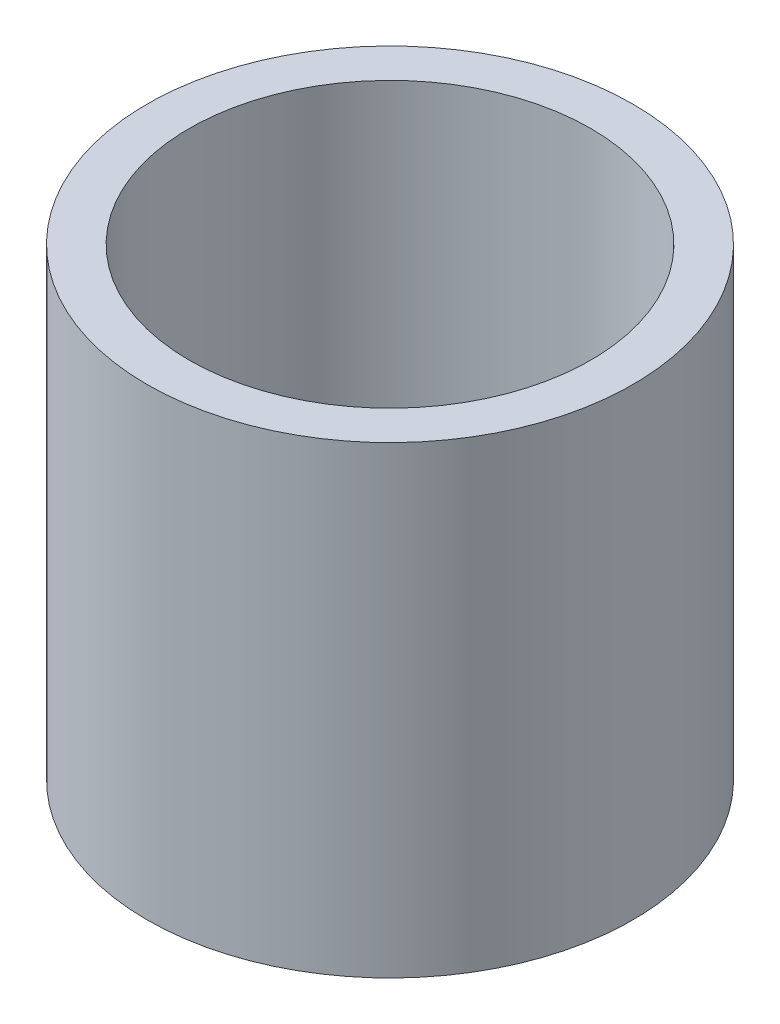
SolidWorks part; units mm, degrees
ref_plane "Front Plane" through (0, 0, 0) normal (0, 0, 1) x (1, 0, 0)
ref_plane "Top Plane" through (0, 0, 0) normal (0, 1, 0) x (1, 0, 0)
ref_plane "Right Plane" through (0, 0, 0) normal (1, 0, 0) x (0, 0, -1)
sketch "Sketch2" plane through (0, 0, 0) normal (0, 1, 0) x (1, 0, 0)
  circle A0 centre (0, 0) radius 5.7625
  dimension "D1" = 11.525
extrude "Boss-Extrude1" add sketch "Sketch2" along normal blind 1
sketch "Sketch3" plane through (0, 1, 0) normal (0, 1, 0) x (1, 0, 0)
  circle A0 centre (0, 0) radius 5.7625
  circle A1 centre (0, 0) radius 4.7625
  dimension "D1" = 9.525
  dimension "D2" = 11.525
extrude "Boss-Extrude2" add sketch "Sketch3" along normal blind 10
